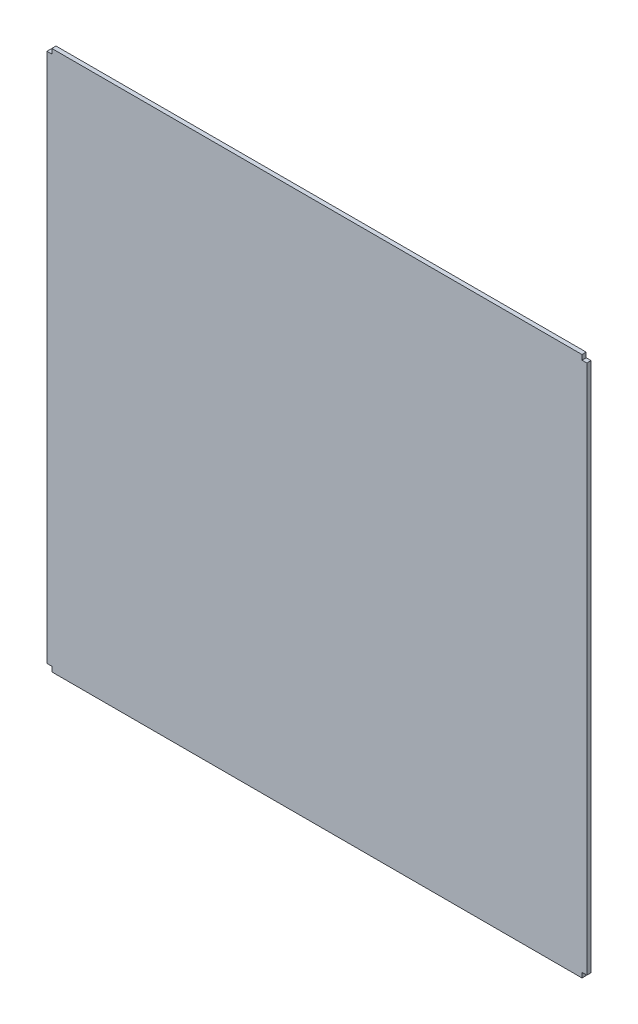
SolidWorks part; units mm, degrees
material "Acrylic (Medium-high impact)"
ref_plane "Front Plane" through (0, 0, 0) normal (0, 0, 1) x (1, 0, 0)
ref_plane "Top Plane" through (0, 0, 0) normal (0, 1, 0) x (1, 0, 0)
ref_plane "Right Plane" through (0, 0, 0) normal (1, 0, 0) x (0, 0, -1)
sketch "Sketch1" plane through (0, 0, 0) normal (0, 0, 1) x (1, 0, 0)
  line L1 (-289.5, -289.5) -> (289.5, -289.5)
  line L2 (-289.5, -289.5) -> (-289.5, 289.5)
  line L3 (-289.5, 289.5) -> (289.5, 289.5)
  line L4 (289.5, -289.5) -> (289.5, 289.5)
  line L5 (-289.5, -289.5) -> (289.5, 289.5) construction
  line L6 (-289.5, 289.5) -> (289.5, -289.5) construction
  point P0 (0, 0)
  dimension "D1" = 579
  dimension "D2" = 579
extrude "Boss-Extrude1" add sketch "Sketch1" along normal mid plane 4.4958
sketch "Sketch2" plane through (0, 0, 2.2479) normal (0, 0, 1) x (1, 0, 0)
  line L0 (-284.75, 303.75) -> (-284.75, 285.75) construction
  line L1 (-285.75, 284.75) -> (-303.75, 284.75) construction
  line L2 (284.75, 285.75) -> (284.75, 303.75) construction
  line L3 (303.75, 284.75) -> (285.75, 284.75) construction
  line L4 (285.75, -284.75) -> (303.75, -284.75) construction
  line L5 (284.75, -303.75) -> (284.75, -285.75) construction
  line L6 (-303.75, -284.75) -> (-285.75, -284.75) construction
  line L7 (-284.75, -285.75) -> (-284.75, -303.75) construction
  line L8 (-284.75, 303.75) -> (-284.75, 284.75) construction
  line L9 (-284.75, 284.75) -> (-303.75, 284.75) construction
  line L10 (284.75, 284.75) -> (284.75, 303.75) construction
  line L11 (303.75, 284.75) -> (284.75, 284.75) construction
  line L12 (284.75, -284.75) -> (303.75, -284.75) construction
  line L13 (284.75, -303.75) -> (284.75, -284.75) construction
  line L14 (-303.75, -284.75) -> (-284.75, -284.75) construction
  line L15 (-284.75, -284.75) -> (-284.75, -303.75) construction
  line L16 (-284.25, 303.75) -> (-284.25, 284.25)
  line L17 (-284.25, 284.25) -> (-303.75, 284.25)
  line L18 (-303.75, -284.25) -> (-284.25, -284.25)
  line L19 (-284.25, -284.25) -> (-284.25, -303.75)
  line L20 (284.25, -303.75) -> (284.25, -284.25)
  line L21 (284.25, -284.25) -> (303.75, -284.25)
  line L22 (303.75, 284.25) -> (284.25, 284.25)
  line L23 (284.25, 284.25) -> (284.25, 303.75)
  line L24 (284.25, 303.75) -> (303.75, 284.25)
  line L25 (303.75, -284.25) -> (284.25, -303.75)
  line L26 (-303.75, -284.25) -> (-284.25, -303.75)
  line L27 (-284.25, 303.75) -> (-303.75, 284.25)
  dimension "D1" = 0.5
  dimension "D2" = 0.5
  dimension "D3" = 0.5
  dimension "D4" = 0.5
extrude "Cut-Extrude1" cut sketch "Sketch2" against normal up to surface (4.4958 mm away) up to face at (0, 0, -2.2479)
